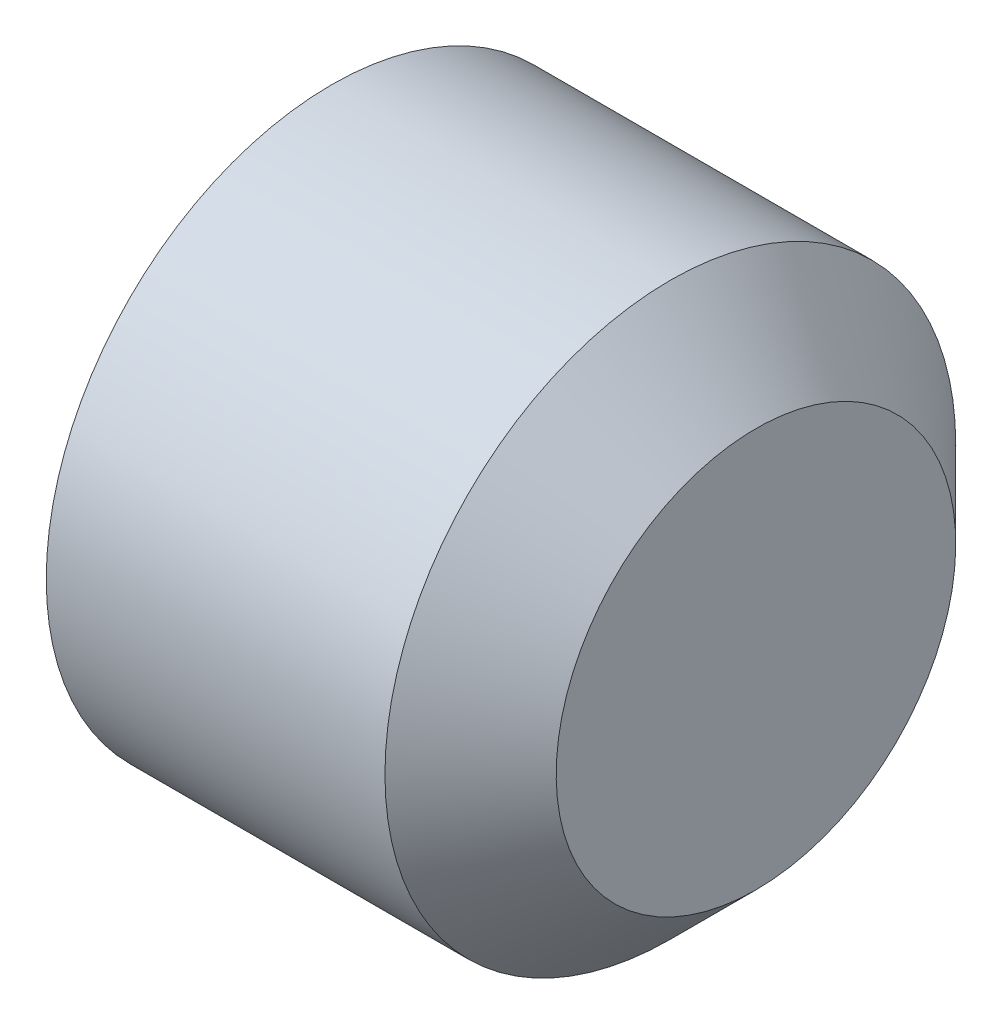
SolidWorks part; units mm, degrees
ref_plane "Front Plane" through (0, 0, 0) normal (0, 0, 1) x (1, 0, 0)
ref_plane "Top Plane" through (0, 0, 0) normal (0, 1, 0) x (1, 0, 0)
ref_plane "Right Plane" through (0, 0, 0) normal (1, 0, 0) x (0, 0, -1)
ref_plane "Plane1" through (0, 0, 0) normal (0, 0, 1) x (1, 0, 0)
sketch "Sketch1" plane through (0, 0, 0) normal (0, 0, 1) x (1, 0, 0)
  line L0 (4, 0) -> (4, -1.75)
  line L1 (4, -1.75) -> (3.25, -2.5)
  line L2 (3.25, -2.5) -> (0.2832, -2.5)
  line L3 (0.2832, -2.5) -> (0, -2.0095)
  line L4 (0, -2.0095) -> (0, -1.4434)
  line L5 (0, -1.4434) -> (0.8333, 0)
  line L6 (0.8333, 0) -> (4, 0)
  line L7 (0.8333, 0) -> (4, 0) construction
revolve "Revolve1" add sketch "Sketch1" angle 360 about L7
ref_plane "Plane2" through (0, 0, 0) normal (1, 0, 0) x (0, 0, -1)
sketch "Sketch2" plane through (0, 0, 0) normal (1, 0, 0) x (0, 0, -1)
  line L0 (-1.4434, 0) -> (-0.7217, -1.25)
  line L1 (-0.7217, -1.25) -> (0.7217, -1.25)
  line L2 (0.7217, -1.25) -> (1.4434, 0)
  line L3 (1.4434, 0) -> (0.7217, 1.25)
  line L4 (0.7217, 1.25) -> (-0.7217, 1.25)
  line L5 (-0.7217, 1.25) -> (-1.4434, 0)
extrude "Cut-Extrude1" cut sketch "Sketch2" along normal blind 2
